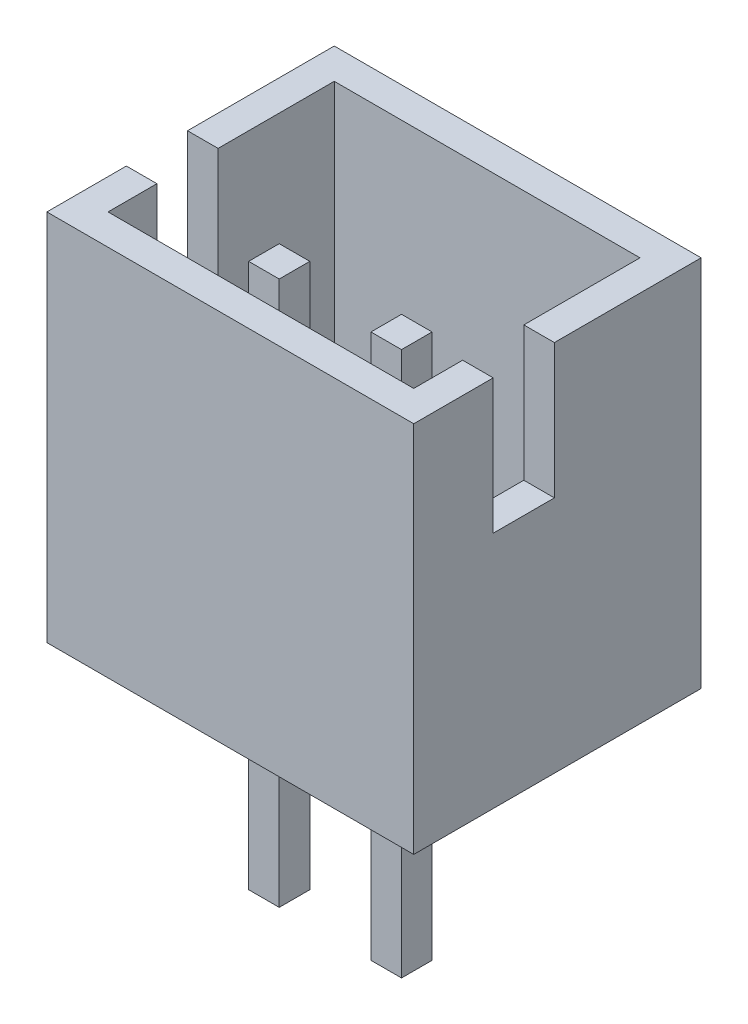
SolidWorks part; units mm, degrees
ref_plane "Front Plane" through (0, 0, 0) normal (0, 0, 1) x (1, 0, 0)
ref_plane "Top Plane" through (0, 0, 0) normal (0, 1, 0) x (1, 0, 0)
ref_plane "Right Plane" through (0, 0, 0) normal (1, 0, 0) x (0, 0, -1)
sketch "Sketch1" plane through (0, 0, 0) normal (0, 1, 0) x (1, 0, 0)
  line L1 (3, -2.35) -> (-3, -2.35)
  line L2 (3, -2.35) -> (3, 2.35)
  line L3 (3, 2.35) -> (-3, 2.35)
  line L4 (-3, -2.35) -> (-3, 2.35)
  line L5 (3, -2.35) -> (-3, 2.35) construction
  line L6 (3, 2.35) -> (-3, -2.35) construction
  point P0 (0, 0)
  dimension "D1" = 4.7
  dimension "D2" = 6
extrude "Boss-Extrude1" add sketch "Sketch1" along normal blind 6.1
shell "Shell1" thickness 0.5
sketch "Sketch2" plane through (0, 0.5, 0) normal (0, 1, 0) x (1, 0, 0)
  line L0 (-2.5, -0.55) -> (2.5, -0.55) construction
  line L1 (-2.5, 1.85) -> (-2.5, -1.85) construction
  line L2 (2.5, -1.85) -> (2.5, 1.85) construction
  line L4 (-3, -2.35) -> (3, -2.35) construction
  line L6 (-0.75, -0.8) -> (-1.25, -0.8)
  line L7 (-0.75, -0.8) -> (-0.75, -0.3)
  line L8 (-0.75, -0.3) -> (-1.25, -0.3)
  line L9 (-1.25, -0.8) -> (-1.25, -0.3)
  line L10 (-0.75, -0.8) -> (-1.25, -0.3) construction
  line L11 (-0.75, -0.3) -> (-1.25, -0.8) construction
  line L12 (0, -2.585) -> (0, 2.585) construction
  line L13 (0.75, -0.3) -> (1.25, -0.3)
  line L14 (1.25, -0.8) -> (1.25, -0.3)
  line L15 (0.75, -0.8) -> (1.25, -0.8)
  line L16 (0.75, -0.8) -> (0.75, -0.3)
  point P8 (-1, -0.55)
  dimension "D1" = 1.8
  dimension "D2" = 0.5
  dimension "D3" = 2
extrude "Boss-Extrude2" add sketch "Sketch2" along normal blind 5 and the other way blind 3.9 separate body
sketch "Sketch3" plane through (-3, 0, 0) normal (-1, 0, 0) x (0, 0, 1)
  line L0 (-2.35, 6.1) -> (2.35, 6.1) construction
  line L1 (1.05, 3.9) -> (0.05, 3.9)
  line L2 (1.05, 3.9) -> (1.05, 6.1)
  line L3 (1.05, 6.1) -> (0.05, 6.1)
  line L4 (0.05, 3.9) -> (0.05, 6.1)
  line L5 (1.05, 3.9) -> (0.05, 6.1) construction
  line L6 (1.05, 6.1) -> (0.05, 3.9) construction
  line L7 (-2.35, 0) -> (2.35, 0) construction
  line L9 (0.3, -3.4) -> (0.8, -3.4) construction
  point P0 (0.55, 5)
  point P11 (0, 0)
  point P14 (0.55, -3.4)
  dimension "D1" = 1
  dimension "D2" = 5
extrude "Cut-Extrude1" cut sketch "Sketch3" against normal up to surface (5.5 mm away)
mirror "Mirror1" about plane through (0, 0, 0) normal (1, 0, 0) of "Cut-Extrude1"
